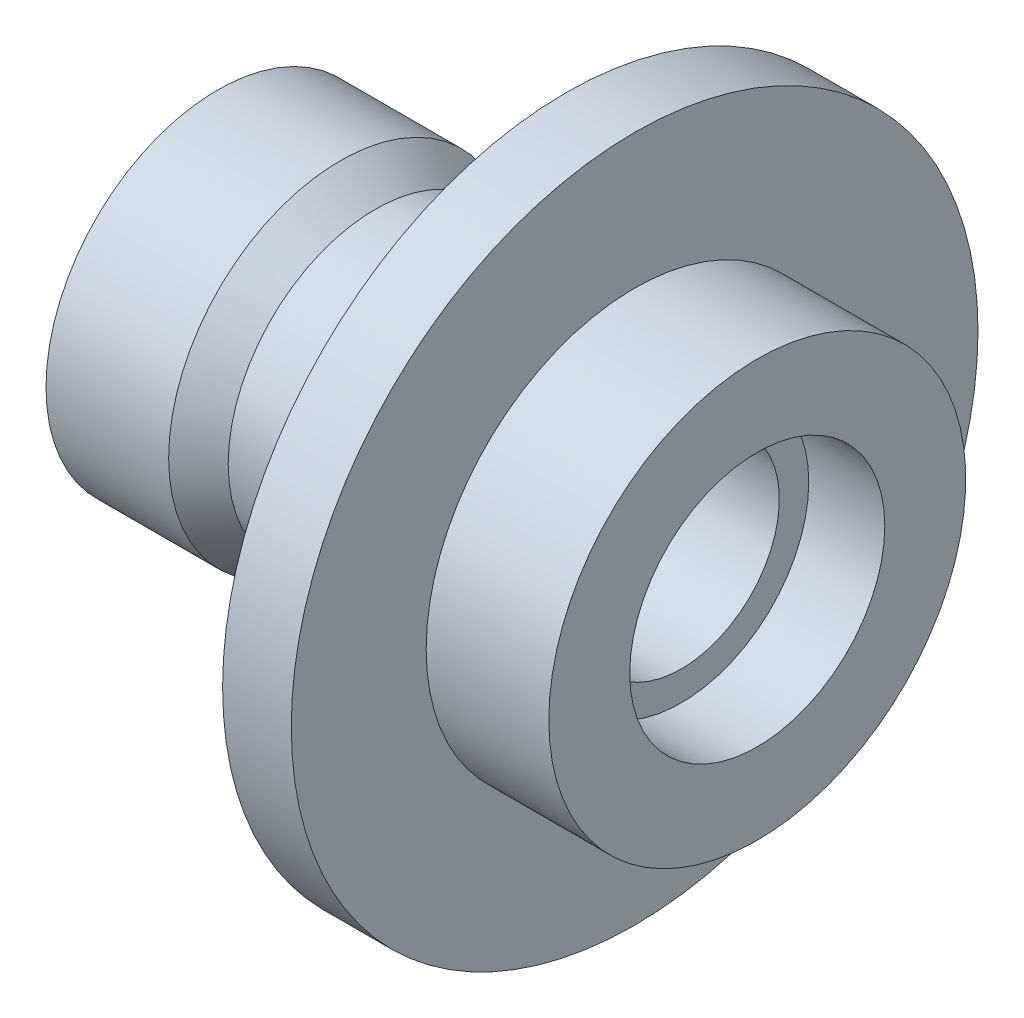
SolidWorks part; units mm, degrees
ref_plane "Piano frontale" through (0, 0, 0) normal (0, 0, 1) x (1, 0, 0)
ref_plane "Piano superiore" through (0, 0, 0) normal (0, 1, 0) x (1, 0, 0)
ref_plane "Piano destro" through (0, 0, 0) normal (1, 0, 0) x (0, 0, -1)
sketch "Schizzo1" plane through (0, 0, 0) normal (0, 0, 1) x (1, 0, 0)
  line L0 (-27.2255, 20) -> (49.4245, 20)
  line L1 (49.4245, 20) -> (49.4245, 26)
  line L2 (49.4245, 26) -> (64.9245, 26)
  line L3 (64.9245, 26) -> (64.9245, 42.5)
  line L4 (64.9245, 42.5) -> (39.9245, 42.5)
  line L5 (39.9245, 42.5) -> (39.9245, 70)
  line L6 (39.9245, 70) -> (25.9245, 70)
  line L7 (25.9245, 70) -> (25.9245, 30)
  line L8 (25.9245, 30) -> (-12.9347, 30)
  line L9 (-12.9347, 30) -> (-20.0755, 35)
  line L10 (-20.0755, 35) -> (-45.0755, 35)
  line L11 (-45.0755, 35) -> (-45.0755, 23.5)
  line L12 (-45.0755, 23.5) -> (-43.0755, 23.5)
  line L13 (-43.0755, 23.5) -> (-43.0755, 24.75)
  line L14 (-43.0755, 24.75) -> (-41.2255, 24.75)
  line L17 (-41.2255, 24.75) -> (-41.2255, 23.5)
  line L18 (-41.2255, 23.5) -> (-27.2255, 23.5)
  line L19 (-27.2255, 23.5) -> (-27.2255, 20)
  dimension "D1" = 14
  dimension "D2" = 25
  dimension "D3" = 71
  dimension "D4" = 25
  dimension "D5" = 20
  dimension "D6" = 30
  dimension "D7" = 15.5
  dimension "D8" = 35
  dimension "D9" = 23.5
  dimension "D10" = 23.5
  dimension "D11" = 24.75
  dimension "D12" = 2
  dimension "D13" = 1.85
  dimension "D14" = 17.85
  dimension "D15" = 110
  dimension "D16" = 26
  dimension "D17" = 42.5
  dimension "D18" = 70
ref_axis "Assi1" through (0, 0, 0) along (1, 0, 0)
revolve "Rivoluzione1" add sketch "Schizzo1" angle 360 about axis through (0, 0, 0) along (1, 0, 0)
fillet "Raccordo1" radius 3 1 edges at (25.9245, 0, 30)
